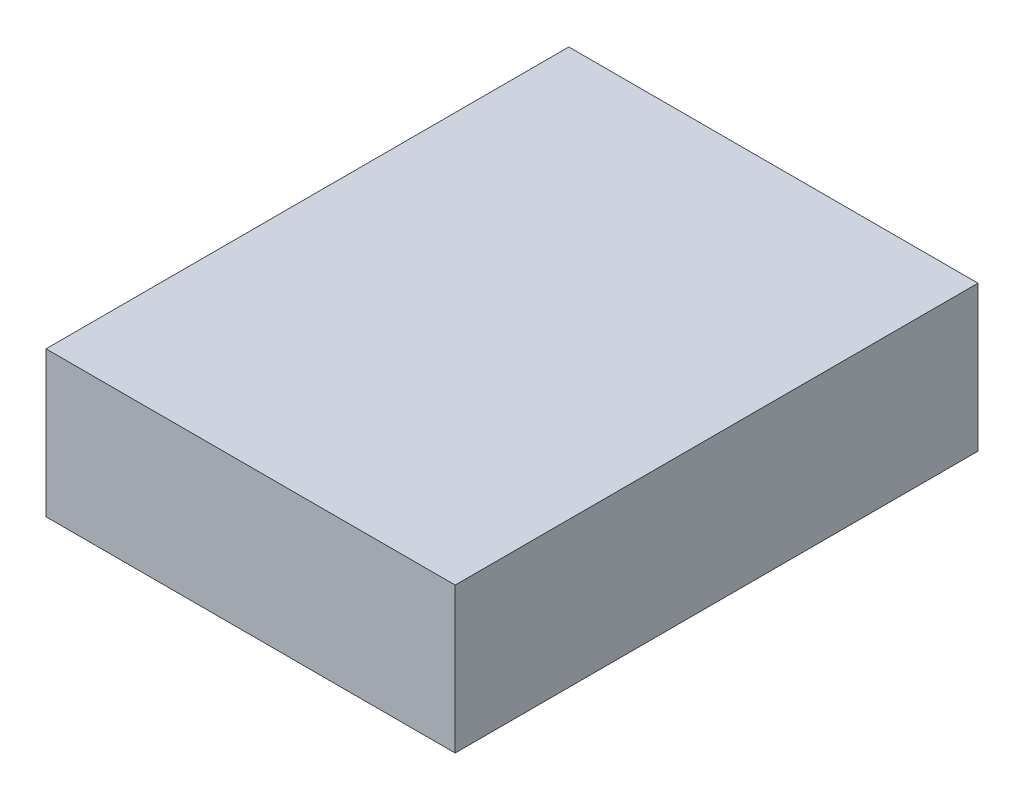
SolidWorks part; units mm, degrees
ref_plane "Płaszczyzna przednia" through (0, 0, 0) normal (0, 0, 1) x (1, 0, 0)
ref_plane "Płaszczyzna górna" through (0, 0, 0) normal (0, 1, 0) x (1, 0, 0)
ref_plane "Płaszczyzna prawa" through (0, 0, 0) normal (1, 0, 0) x (0, 0, -1)
sketch "Sketch1" plane through (0, 0, 0) normal (0, 1, 0) x (1, 0, 0)
  line L1 (-45, -57.5) -> (45, -57.5)
  line L2 (-45, -57.5) -> (-45, 57.5)
  line L3 (-45, 57.5) -> (45, 57.5)
  line L4 (45, -57.5) -> (45, 57.5)
  line L5 (-45, -57.5) -> (45, 57.5) construction
  line L6 (-45, 57.5) -> (45, -57.5) construction
  point P0 (0, 0)
  dimension "D1" = 90
  dimension "D2" = 115
extrude "Boss-Extrude1" add sketch "Sketch1" along normal blind 32
